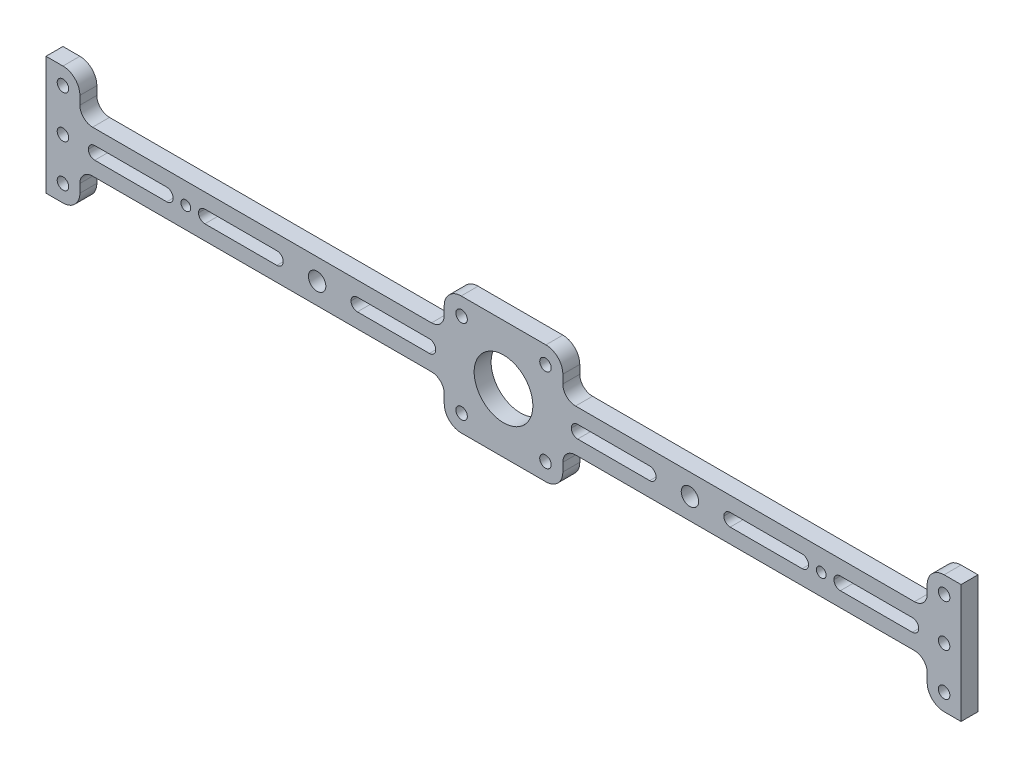
SolidWorks part; units mm, degrees
material "6061-T6 (SS)"
ref_plane "Front" through (0, 0, 0) normal (0, 0, 1) x (1, 0, 0)
ref_plane "Top" through (0, 0, 0) normal (0, 1, 0) x (1, 0, 0)
ref_plane "Right" through (0, 0, 0) normal (1, 0, 0) x (0, 0, -1)
sketch "Sketch4" plane through (0, 0, 0) normal (0, 0, 1) x (1, 0, 0)
  line L0 (-165.1, 0) -> (0, 0) construction
  line L1 (-158.75, -7.9375) -> (158.75, -7.9375)
  line L2 (-158.75, -7.9375) -> (-158.75, 7.9375)
  line L3 (-158.75, 7.9375) -> (158.75, 7.9375)
  line L4 (158.75, -7.9375) -> (158.75, 7.9375)
  line L5 (-158.75, -7.9375) -> (158.75, 7.9375) construction
  line L6 (-158.75, 7.9375) -> (158.75, -7.9375) construction
  line L7 (-171.45, -22.225) -> (-158.75, -22.225)
  line L8 (-171.45, -22.225) -> (-171.45, 22.225)
  line L9 (-171.45, 22.225) -> (-158.75, 22.225)
  line L10 (-158.75, -22.225) -> (-158.75, 22.225)
  line L11 (-171.45, -22.225) -> (-158.75, 22.225) construction
  line L12 (-171.45, 22.225) -> (-158.75, -22.225) construction
  line L17 (171.45, 22.225) -> (158.75, 22.225)
  line L18 (171.45, 22.225) -> (171.45, -22.225)
  line L19 (171.45, -22.225) -> (158.75, -22.225)
  line L20 (158.75, 22.225) -> (158.75, -22.225)
  line L21 (171.45, 22.225) -> (158.75, -22.225) construction
  line L22 (171.45, -22.225) -> (158.75, 22.225) construction
  line L23 (0, 0) -> (165.1, 0) construction
  line L25 (-22.225, 22.225) -> (22.225, 22.225)
  line L26 (-22.225, 22.225) -> (-22.225, -22.225)
  line L27 (-22.225, -22.225) -> (22.225, -22.225)
  line L28 (22.225, 22.225) -> (22.225, -22.225)
  line L29 (-22.225, 22.225) -> (22.225, -22.225) construction
  line L30 (-22.225, -22.225) -> (22.225, 22.225) construction
  point P0 (0, 0)
  point P6 (-165.1, 0)
  point P12 (165.1, 0)
  dimension "D1" = 342.9
  dimension "D2" = 12.7
  dimension "D3" = 44.45
  dimension "D4" = 15.875
  dimension "D5" = 44.45
extrude "Boss-Extrude2" add sketch "Sketch4" along normal blind 6.35 contours L7 L10 L2 L9 L8 | L26 L3 L2 L1 | L28 L25 L26 L3 | L28 L3 L26 L1 | L28 L1 L26 L27 | L3 L28 L1 L4 | L17 L20 L4 L19 L18
fillet "Fillet4" radius 4.7625 8 edges at (158.75, 7.9375, 3.175) (158.75, -7.9375, 3.175) (-158.75, -7.9375, 3.175) (-158.75, 7.9375, 3.175) (-22.225, -7.9375, 3.175) (-22.225, 7.9375, 3.175) (22.225, -7.9375, 3.175) (22.225, 7.9375, 3.175)
fillet "Fillet5" radius 6.35 8 edges at (-158.75, 22.225, 3.175) (-158.75, -22.225, 3.175) (158.75, -22.225, 3.175) (158.75, 22.225, 3.175) (22.225, 22.225, 3.175) (-22.225, 22.225, 3.175) (-22.225, -22.225, 3.175) (22.225, -22.225, 3.175)
sketch "Sketch5" plane through (0, 0, 6.35) normal (0, 0, 1) x (1, 0, 0)
  line L0 (-165.1, 22.225) -> (-165.1, -22.225) construction
  line L1 (-171.45, 22.225) -> (-165.1, 22.225) construction
  line L2 (-171.45, -22.225) -> (-165.1, -22.225) construction
  line L3 (-171.45, -22.225) -> (-171.45, 22.225) construction
  circle A0 centre (0, 0) radius 11
  dimension "D3" = 22
  dimension "D1" = 6.35
sketch "Sketch7" plane through (0, 0, 6.35) normal (0, 0, 1) x (1, 0, 0)
  line L0 (-171.45, 0) -> (171.45, 0) construction
  line L1 (-171.45, -22.225) -> (-171.45, 22.225) construction
  line L2 (171.45, 22.225) -> (171.45, -22.225) construction
  line L4 (-153.194, 2.3812) -> (-126.206, 2.3813)
  line L5 (-155.575, 0.0003) -> (-155.575, -0.0003)
  line L6 (-153.194, -2.3813) -> (-126.206, -2.3812)
  line L7 (-123.825, 0.0003) -> (-123.825, -0.0003)
  line L8 (-155.575, 2.3813) -> (-123.825, -2.3812) construction
  line L9 (-155.575, -2.3813) -> (-123.825, 2.3813) construction
  arc A0 (-126.206, 2.3813) -> (-123.825, 0.0003) centre (-126.206, 0.0003) cw
  arc A1 (-126.206, -2.3812) -> (-123.825, -0.0003) centre (-126.206, -0.0003) ccw
  arc A2 (-155.575, -0.0003) -> (-153.194, -2.3813) centre (-153.194, -0.0003) ccw
  arc A3 (-153.194, 2.3812) -> (-155.575, 0.0003) centre (-153.194, 0.0003) ccw
  point P6 (-139.7, 0)
  dimension "D3" = 2.381
  dimension "D1" = 15.875
  dimension "D2" = 4.7625
  dimension "D4" = 31.75
extrude "Cut-Extrude3" cut sketch "Sketch7" against normal blind 6.35
hole_wizard "#18 (0.1695) Diameter Hole1" positions "Sketch10" profile "Sketch11" hole size "#18" standard "ANSI Inch" end condition through all
sketch "Sketch10" plane through (0, 0, 6.35) normal (0, 0, 1) x (1, 0, 0)
  line L0 (-171.45, 0) -> (-165.1, 0) construction
  line L1 (-171.45, -22.225) -> (-171.45, 22.225) construction
  line L3 (-165.1, 15.875) -> (-165.1, 0) construction
  line L5 (-165.1, 0) -> (-165.1, -15.875) construction
  point P0 (-165.1, 15.875)
  point P2 (-165.1, 0)
  point P4 (-165.1, -15.875)
  dimension "D1" = 15.875
  dimension "D2" = 6.35
sketch "Sketch11" plane through (-165.1, 15.875, 6.35) normal (1, 0, 0) x (0, -1, 0)
  line L0 (0, 0) -> (0, 6.35)
  line L1 (0, 6.35) -> (2.1526, 6.35)
  line L2 (2.1526, 6.35) -> (2.1526, 0)
  line L5 (2.1526, 0) -> (0, 0)
  line L11 (0, -6.35) -> (0, 107.95) construction
  dimension "Thru Hole Dia." = 4.3053
  dimension "Thru Hole Depth" = 6.35
hole_wizard "#18 (0.1695) Diameter Hole2" positions "Sketch16" profile "Sketch15" hole size "#18" standard "ANSI Inch" end condition through all
sketch "Sketch16" plane through (0, 0, 0) normal (0, 0, -1) x (-1, 0, 0)
  line L0 (0, 0) -> (-15.7154, -15.7154) construction
  line L2 (0, 0) -> (-15.7154, 15.7154) construction
  line L4 (0, 0) -> (-57.15, 0) construction
  circle A0 centre (0, 0) radius 22.225 construction
  point P0 (-15.7154, -15.7154)
  point P9 (-15.7154, 15.7154)
  dimension "D1" = 44.45
  dimension "D2" = 57.15
sketch "Sketch15" plane through (15.7154, -15.7154, 0) normal (1, 0, 0) x (0, 1, 0)
  line L0 (0, 0) -> (0, 6.35)
  line L1 (0, 6.35) -> (2.1526, 6.35)
  line L2 (2.1526, 6.35) -> (2.1526, 0)
  line L5 (2.1526, 0) -> (0, 0)
  line L11 (0, -6.35) -> (0, 107.95) construction
  dimension "Thru Hole Dia." = 4.3053
  dimension "Thru Hole Depth" = 6.35
pattern_linear "LPattern1" count 2 spacing 41.275 along (1, 0, 0) of "Cut-Extrude3"
hole_wizard "F (0.257) Diameter Hole1" positions "Sketch19" profile "Sketch18" hole size "F" standard "ANSI Inch" end condition through all
sketch "Sketch19" plane through (0, 0, 0) normal (0, 0, -1) x (-1, 0, 0)
  line L0 (-69.85, 0) -> (0, 0) construction
  point P0 (-69.85, 0)
  dimension "D1" = 69.85
sketch "Sketch18" plane through (69.85, 0, 0) normal (1, 0, 0) x (0, 1, 0)
  line L0 (0, 0) -> (0, 6.35)
  line L1 (0, 6.35) -> (3.2639, 6.35)
  line L2 (3.2639, 6.35) -> (3.2639, 0)
  line L5 (3.2639, 0) -> (0, 0)
  line L11 (0, -6.35) -> (0, 107.95) construction
  dimension "Thru Hole Dia." = 6.5278
  dimension "Thru Hole Depth" = 6.35
extrude "Cut-Extrude4" cut sketch "Sketch5" against normal through all
pattern_linear "LPattern2" count 2 spacing 98.425 along (1, 0, 0) of "Cut-Extrude3"
mirror "Mirror1" about plane through (0, 0, 0) normal (1, 0, 0) of "LPattern2", "#18 (0.1695) Diameter Hole2", "LPattern1", "#18 (0.1695) Diameter Hole1", "F (0.257) Diameter Hole1", "Cut-Extrude3"
sketch "Sketch20" plane through (0, 0, 0) normal (0, 0, -1) x (-1, 0, 0)
  line L0 (-123.825, -0.0003) -> (-114.3, -0.0003) construction
  circle A0 centre (-119.0625, -0.0003) radius 1.8288
  dimension "D1" = 3.6576
extrude "Cut-Extrude5" cut sketch "Sketch20" against normal through all
mirror "Mirror2" about plane through (0, 0, 0) normal (1, 0, 0) of "Cut-Extrude5"
